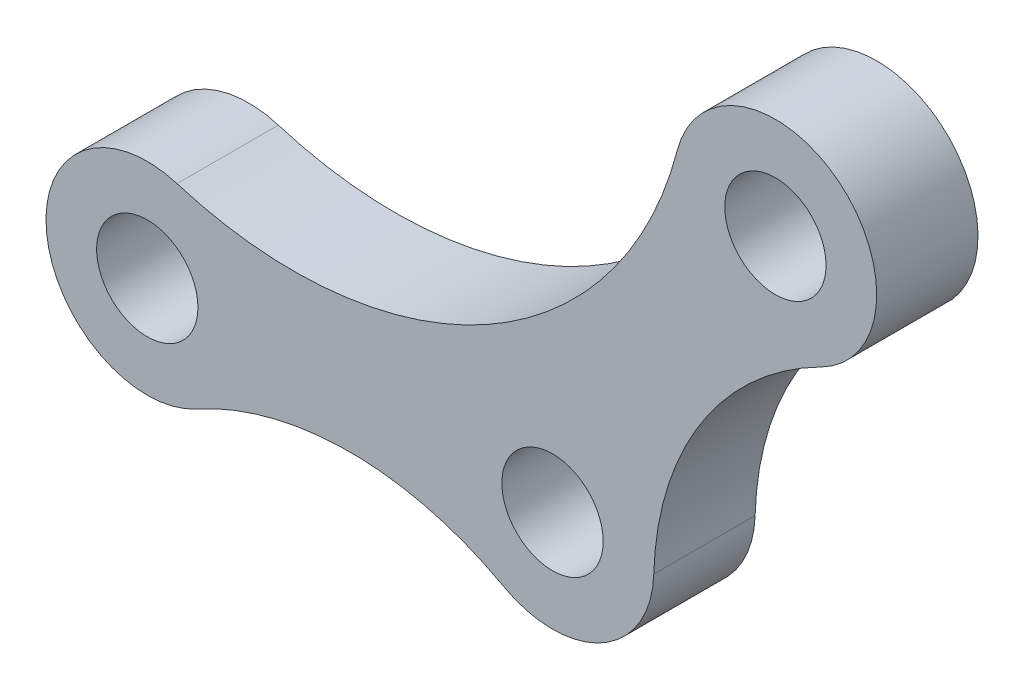
SolidWorks part; units mm, degrees
ref_plane "前基準面" through (0, 0, 0) normal (0, 0, 1) x (1, 0, 0)
ref_plane "上基準面" through (0, 0, 0) normal (0, 1, 0) x (1, 0, 0)
ref_plane "右基準面" through (0, 0, 0) normal (1, 0, 0) x (0, 0, -1)
sketch "草圖1" plane through (0, 0, 0) normal (0, 0, 1) x (1, 0, 0)
  line L0 (0, 0) -> (31, 17.2988) construction
  line L1 (31, 17.2988) -> (20, 0) construction
  line L2 (20, 0) -> (0, 0) construction
  line L3 (28.5635, 21.665) -> (-2.4365, 4.3662)
  line L4 (0, -5) -> (20, -5)
  line L5 (24.2192, -2.6829) -> (35.2192, 14.6159)
  circle A0 centre (0, 0) radius 2.5
  circle A1 centre (20, 0) radius 2.5
  circle A2 centre (31, 17.2988) radius 2.5
  arc A3 (35.2192, 14.6159) -> (28.5635, 21.665) centre (31, 17.2988) ccw
  arc A4 (20, -5) -> (24.2192, -2.6829) centre (20, 0) ccw
  arc A5 (-2.4365, 4.3662) -> (0, -5) centre (0, 0) ccw
  circle A6 centre (20, 0) radius 5 construction
  circle A7 centre (0, 0) radius 5 construction
  circle A8 centre (31, 17.2988) radius 5 construction
  dimension "D4" = 5
  dimension "D1" = 35.5
  dimension "D2" = 20.5
  dimension "D3" = 20
  dimension "D5" = 2.5
extrude "填料-伸長1" add sketch "草圖1" along normal mid plane 5
sketch "草圖2" plane through (0, 0, 2.5) normal (0, 0, 1) x (1, 0, 0)
  arc A0 (-2.4365, 4.3662) -> (0, -5) centre (0, 0) ccw construction
  arc A1 (20, -5) -> (24.2192, -2.6829) centre (20, 0) ccw construction
  arc A2 (35.2192, 14.6159) -> (28.5635, 21.665) centre (31, 17.2988) ccw construction
  arc A3 (1.4668, 4.78) -> (2.4167, -4.3772) centre (0, 0) ccw
  arc A4 (17.5833, -4.3772) -> (24.9979, -0.1434) centre (20, 0) ccw
  arc A5 (33.2497, 12.8336) -> (26.1618, 18.5605) centre (31, 17.2988) ccw
  arc A6 (2.4167, -4.3772) -> (17.5833, -4.3772) centre (10, -18.1122) cw
  arc A7 (24.9979, -0.1434) -> (33.2497, 12.8336) centre (40.0049, -0.574) cw
  arc A8 (26.1618, 18.5605) -> (1.4668, 4.78) centre (7.2119, 23.5019) cw
extrude "除料-伸長1" cut sketch "草圖2" against normal blind 5 flip side to cut
